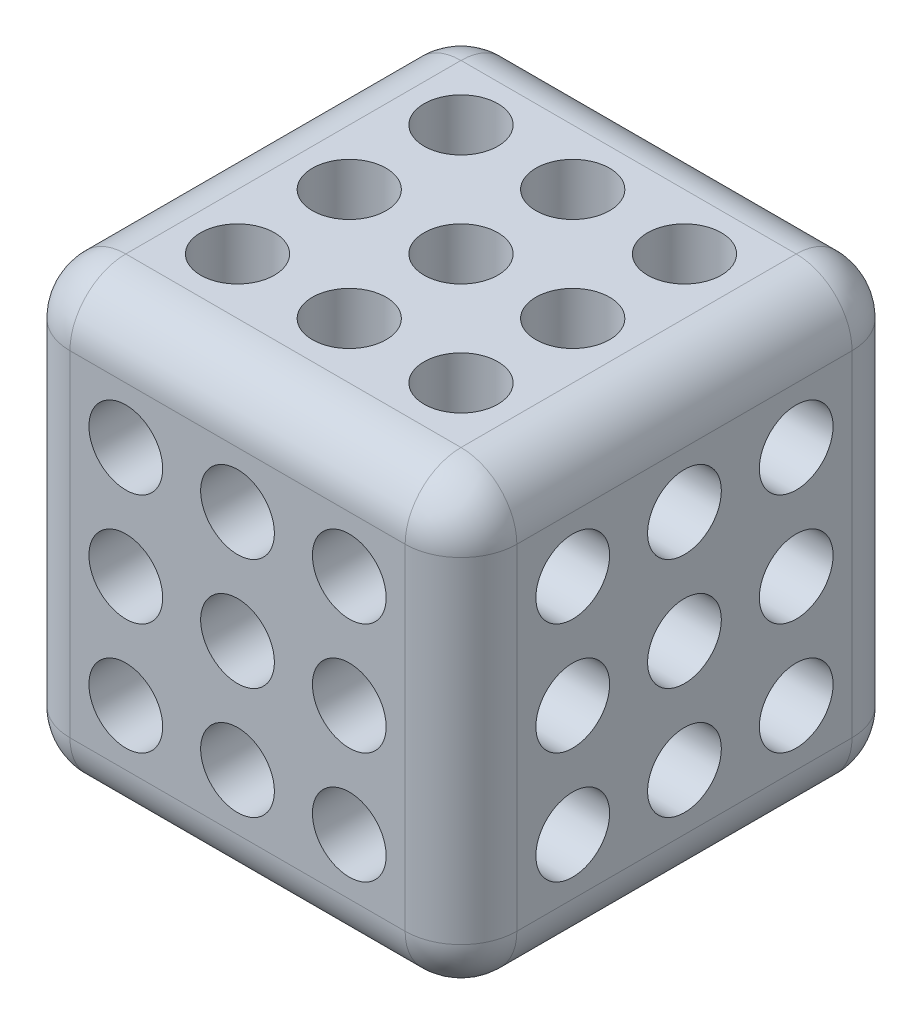
SolidWorks part; units mm, degrees
material "1.0736 (11SMn37)"
ref_plane "Plan de face" through (0, 0, 0) normal (0, 0, 1) x (1, 0, 0)
ref_plane "Plan de dessus" through (0, 0, 0) normal (0, 1, 0) x (1, 0, 0)
ref_plane "Plan de droite" through (0, 0, 0) normal (1, 0, 0) x (0, 0, -1)
sketch "Esquisse1" plane through (0, 0, 0) normal (1, 0, 0) x (0, 0, -1)
  line L1 (10, -10) -> (-10, -10)
  line L2 (10, -10) -> (10, 10)
  line L3 (10, 10) -> (-10, 10)
  line L4 (-10, -10) -> (-10, 10)
  line L5 (10, -10) -> (-10, 10) construction
  line L6 (10, 10) -> (-10, -10) construction
  point P0 (0, 0)
  dimension "D1" = 20
  dimension "D2" = 20
extrude "Boss.-Extru.1" add sketch "Esquisse1" along normal mid plane 20
hole_wizard "Trou taraudé M41" positions "Esquisse2" profile "Esquisse3" tap size "M4" standard "ISO"
sketch "Esquisse2" plane through (10, 0, 0) normal (1, 0, 0) x (0, 0, -1)
  line L0 (-5, 5) -> (5, 5) construction
  line L1 (5, 5) -> (5, -5) construction
  line L2 (5, -5) -> (-5, -5) construction
  line L3 (-5, -5) -> (-5, 5) construction
  point P0 (-5, 5)
  point P2 (0, 5)
  point P4 (5, 5)
  point P6 (5, 0)
  point P8 (0, 0)
  point P11 (-5, 0)
  point P13 (-5, -5)
  point P15 (0, -5)
  point P17 (5, -5)
  dimension "D1" = 5
  dimension "D2" = 5
cosmetic thread "Filetage de perçage1" parameters "D2"=4
cosmetic thread "Filetage de perçage2" parameters "D2"=4
cosmetic thread "Filetage de perçage3" parameters "D2"=4
cosmetic thread "Filetage de perçage4" parameters "D2"=4
cosmetic thread "Filetage de perçage5" parameters "D2"=4
cosmetic thread "Filetage de perçage6" parameters "D2"=4
cosmetic thread "Filetage de perçage7" parameters "D2"=4
cosmetic thread "Filetage de perçage8" parameters "D2"=4
cosmetic thread "Filetage de perçage9" parameters "D2"=4
sketch "Esquisse3" plane through (10, 5, 5) normal (0, 1, 0) x (0, 0, -1)
  line L0 (0, 0) -> (0, 10.9914)
  line L1 (0, 10.9914) -> (1.65, 10)
  line L2 (1.65, 10) -> (1.65, 0)
  line L5 (1.65, 0) -> (0, 0)
  line L10 (0, 10.9914) -> (-1.65, 10) construction
  line L11 (0, -6.35) -> (0, 107.95) construction
  dimension "Diamètre du trou pour taraudage" = 3.3
  dimension "Profondeur du trou pour taraudage" = 10
  dimension "Angle de pointe" = 118
hole_wizard "Trou taraudé M43" positions "Esquisse9" profile "Esquisse10" tap size "M4" standard "ISO"
sketch "Esquisse9" plane through (0, 0, 10) normal (0, 0, 1) x (1, 0, 0)
  line L1 (-5, -5) -> (5, -5)
  line L2 (-5, -5) -> (-5, 5)
  line L3 (-5, 5) -> (5, 5)
  line L4 (5, -5) -> (5, 5)
  line L5 (-5, -5) -> (5, 5) construction
  line L6 (-5, 5) -> (5, -5) construction
  point P1 (0, 0)
  point P2 (5, 5)
  point P33 (-5, -5)
  point P34 (-5, 5)
  point P35 (5, -5)
  point P42 (0, 5)
  point P46 (5, 0)
  point P50 (0, -5)
  point P54 (-5, 0)
  dimension "D1" = 5
  dimension "D2" = 5
cosmetic thread "Filetage de perçage19" parameters "D2"=4
cosmetic thread "Filetage de perçage20" parameters "D2"=4
cosmetic thread "Filetage de perçage21" parameters "D2"=4
cosmetic thread "Filetage de perçage22" parameters "D2"=4
cosmetic thread "Filetage de perçage23" parameters "D2"=4
cosmetic thread "Filetage de perçage24" parameters "D2"=4
cosmetic thread "Filetage de perçage25" parameters "D2"=4
cosmetic thread "Filetage de perçage26" parameters "D2"=4
cosmetic thread "Filetage de perçage27" parameters "D2"=4
sketch "Esquisse10" plane through (0, 0, 10) normal (1, 0, 0) x (0, -1, 0)
  line L0 (0, 0) -> (0, 10.9914)
  line L1 (0, 10.9914) -> (1.65, 10)
  line L2 (1.65, 10) -> (1.65, 0)
  line L5 (1.65, 0) -> (0, 0)
  line L10 (0, 10.9914) -> (-1.65, 10) construction
  line L11 (0, -6.35) -> (0, 107.95) construction
  dimension "Diamètre du trou pour taraudage" = 3.3
  dimension "Profondeur du trou pour taraudage" = 10
  dimension "Angle de pointe" = 118
hole_wizard "Trou taraudé M44" positions "Esquisse11" profile "Esquisse12" tap size "M4" standard "ISO"
sketch "Esquisse11" plane through (0, -10, 0) normal (0, -1, 0) x (-1, 0, 0)
  line L1 (-5, -5) -> (5, -5)
  line L2 (-5, -5) -> (-5, 5)
  line L3 (-5, 5) -> (5, 5)
  line L4 (5, -5) -> (5, 5)
  line L5 (-5, -5) -> (5, 5) construction
  line L6 (-5, 5) -> (5, -5) construction
  point P0 (0, 0)
  point P4 (0, 0)
  point P5 (5, 5)
  point P36 (-5, -5)
  point P37 (-5, 5)
  point P38 (5, -5)
  point P44 (0, 5)
  point P48 (5, 0)
  point P52 (0, -5)
  point P56 (-5, 0)
  dimension "D1" = 5
  dimension "D2" = 5
cosmetic thread "Filetage de perçage28" parameters "D2"=4
cosmetic thread "Filetage de perçage29" parameters "D2"=4
cosmetic thread "Filetage de perçage30" parameters "D2"=4
cosmetic thread "Filetage de perçage31" parameters "D2"=4
cosmetic thread "Filetage de perçage32" parameters "D2"=4
cosmetic thread "Filetage de perçage33" parameters "D2"=4
cosmetic thread "Filetage de perçage34" parameters "D2"=4
cosmetic thread "Filetage de perçage35" parameters "D2"=4
cosmetic thread "Filetage de perçage37" parameters "D2"=4
sketch "Esquisse12" plane through (0, -10, 0) normal (1, 0, 0) x (0, 0, -1)
  line L0 (0, 0) -> (0, 10.9914)
  line L1 (0, 10.9914) -> (1.65, 10)
  line L2 (1.65, 10) -> (1.65, 0)
  line L5 (1.65, 0) -> (0, 0)
  line L10 (0, 10.9914) -> (-1.65, 10) construction
  line L11 (0, -6.35) -> (0, 107.95) construction
  dimension "Diamètre du trou pour taraudage" = 3.3
  dimension "Profondeur du trou pour taraudage" = 10
  dimension "Angle de pointe" = 118
fillet "Congé1" radius 2.5 12 edges at (0, -10, -10) (-10, 0, 10) (-10, 0, -10) (-10, -10, 0) (0, -10, 10) (10, -10, 0) (10, 0, 10) (10, 0, -10) (-10, 10, 0) (0, 10, -10) (0, 10, 10) (10, 10, 0)
mirror "Symétrie1" about plane through (0, 0, 0) normal (1, 0, 0) of "Trou taraudé M41"
cosmetic thread "Filetage de perçage39" parameters "D1"=30, "D2"=4
cosmetic thread "Filetage de perçage40" parameters "D1"=30, "D2"=4
cosmetic thread "Filetage de perçage41" parameters "D1"=30, "D2"=4
cosmetic thread "Filetage de perçage42" parameters "D1"=30, "D2"=4
cosmetic thread "Filetage de perçage43" parameters "D1"=30, "D2"=4
cosmetic thread "Filetage de perçage44" parameters "D1"=30, "D2"=4
cosmetic thread "Filetage de perçage45" parameters "D1"=30, "D2"=4
cosmetic thread "Filetage de perçage46" parameters "D1"=30, "D2"=4
cosmetic thread "Filetage de perçage47" parameters "D1"=30, "D2"=4
mirror "Symétrie2" about plane through (0, 0, 0) normal (0, 0, 1) of "Trou taraudé M43"
cosmetic thread "Filetage de perçage48" parameters "D1"=8, "D2"=4
cosmetic thread "Filetage de perçage49" parameters "D1"=8, "D2"=4
cosmetic thread "Filetage de perçage50" parameters "D1"=8, "D2"=4
cosmetic thread "Filetage de perçage51" parameters "D1"=8, "D2"=4
cosmetic thread "Filetage de perçage52" parameters "D1"=8, "D2"=4
cosmetic thread "Filetage de perçage53" parameters "D1"=8, "D2"=4
cosmetic thread "Filetage de perçage54" parameters "D1"=8, "D2"=4
cosmetic thread "Filetage de perçage55" parameters "D1"=8, "D2"=4
mirror "Symétrie3" about plane through (0, 0, 0) normal (0, 1, 0) of "Trou taraudé M44"
cosmetic thread "Filetage de perçage56" parameters "D1"=30, "D2"=4
cosmetic thread "Filetage de perçage57" parameters "D1"=30, "D2"=4
cosmetic thread "Filetage de perçage58" parameters "D1"=30, "D2"=4
cosmetic thread "Filetage de perçage59" parameters "D1"=30, "D2"=4
cosmetic thread "Filetage de perçage60" parameters "D1"=30, "D2"=4
cosmetic thread "Filetage de perçage61" parameters "D1"=30, "D2"=4
cosmetic thread "Filetage de perçage62" parameters "D1"=30, "D2"=4
cosmetic thread "Filetage de perçage63" parameters "D1"=30, "D2"=4
cosmetic thread "Filetage de perçage64" parameters "D1"=30, "D2"=4
